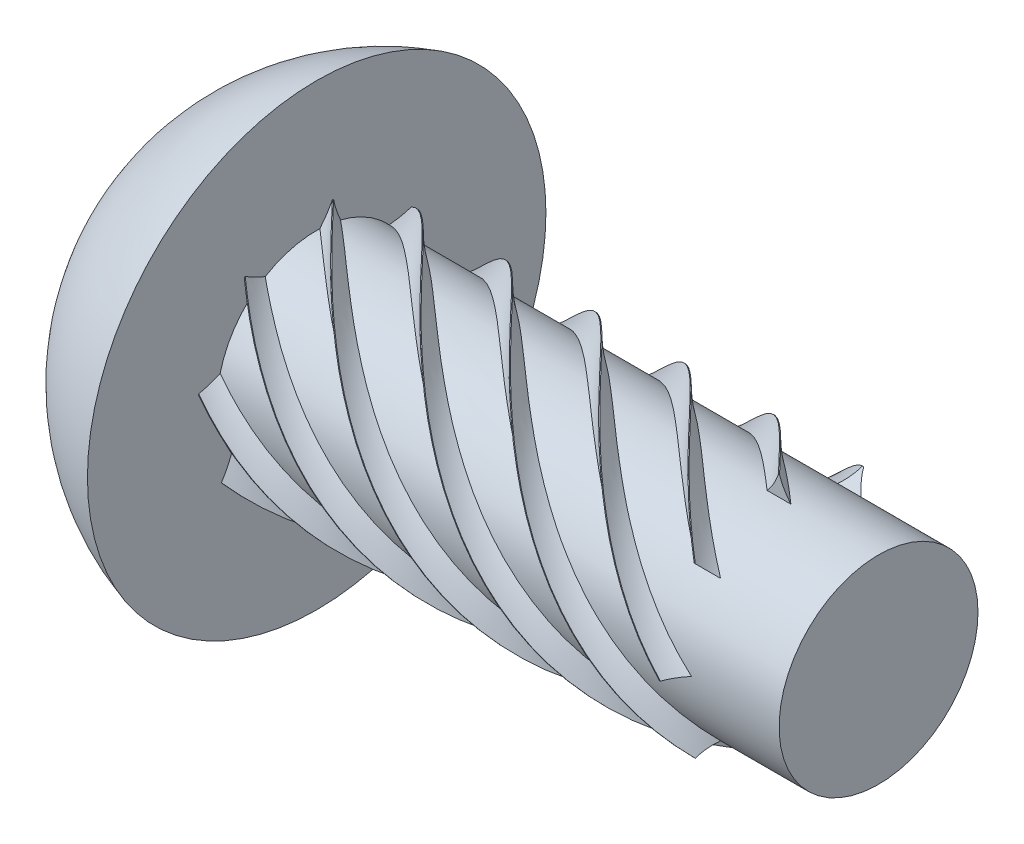
SolidWorks part; units mm, degrees
material "AISI 1020"
ref_plane "Front Plane" through (0, 0, 0) normal (0, 0, 1) x (1, 0, 0)
ref_plane "Top Plane" through (0, 0, 0) normal (0, 1, 0) x (1, 0, 0)
ref_plane "Right Plane" through (0, 0, 0) normal (1, 0, 0) x (0, 0, -1)
sketch "Sketch1" plane through (0, 0, 0) normal (0, 0, 1) x (1, 0, 0)
  line L0 (8.2931, 0) -> (-8.2931, 0) construction
  line L1 (8.2931, -2.2479) -> (8.2931, 2.2479) construction
  line L2 (6.3119, -2.6924) -> (6.3119, 2.6924) construction
  line L3 (-4.4069, -5.1816) -> (-4.4069, 5.1816) construction
  line L4 (0, -101.6) -> (0, 101.6) construction
  point P4 (0, 0)
  point P7 (8.2931, 0)
  point P11 (6.3119, 0)
  point P14 (-4.4069, 0)
  point P17 (0, 0)
  dimension "Shank Diameter" = 5.3848
  dimension "Head Diameter" = 10.3632
  dimension "Head Height" = 3.8862
  dimension "Pilot Diameter" = 4.4958
  dimension "Length" = 12.7
  dimension "Pilot Length" = 1.9812
  dimension "Number of Thread Starts" = 203.2
sketch "Sketch2" plane through (0, 0, 0) normal (0, 0, 1) x (1, 0, 0)
  line L0 (6.3119, -2.6924) -> (6.3119, 2.6924) construction
  line L1 (8.2931, 0) -> (-8.2931, 0) construction
  line L2 (8.2931, 0) -> (8.2931, 2.2479)
  line L3 (8.2931, 2.2479) -> (6.3119, 2.2479)
  line L4 (8.2931, 0) -> (-8.2931, 0) construction
  line L5 (-4.4069, 2.6924) -> (-4.4069, 5.1816)
  line L8 (6.3119, 2.2479) -> (6.3119, 2.6924)
  line L9 (6.3119, 2.6924) -> (-4.4069, 2.6924)
  line L10 (-3.6132, -2.6924) -> (-3.6132, 2.6924) construction
  line L11 (-8.2931, 0) -> (8.2931, 0)
  arc A0 (-4.4069, 5.1816) -> (-8.2931, 0) centre (-2.8956, 0) ccw
  point P7 (-3.6132, -2.6924)
  point P17 (-3.6132, 0)
  dimension "Head Diameter" = 10.3632
  dimension "Head Height" = 3.8862
  dimension "Pilot Diameter" = 4.4958
  dimension "Length" = 12.7
  dimension "D1" = 0.7937
  dimension "Outside Diameter" = 5.3848
revolve "Revolve1" add sketch "Sketch2" angle 360 about L1
sketch "Sketch3" plane through (6.3119, 0, 0) normal (1, 0, 0) x (0, 0, -1)
  circle A0 centre (0, 0) radius 2.6924 construction
  circle A1 centre (0, 0) radius 2.6924
curve "Helix/Spiral1" pitch 16.1544 height 10.7188 turns 0.6635
sketch "Sketch4" plane through (6.3119, 0, 0) normal (1, 0, 0) x (0, 0, -1)
  circle A0 centre (0, 0) radius 2.2479 construction
  circle A1 centre (0, 0) radius 2.6924 construction
  circle A2 centre (0, 0) radius 2.2479
  circle A3 centre (0, 0) radius 2.6924
extrude "Cut-Extrude1" cut sketch "Sketch4" against normal up to surface (10.7188 mm away) up to face at (-4.4069, 0, -5.1816)
sketch "Sketch6" plane through (0, 0, 0) normal (0, 0, 1) x (1, 0, 0)
  line L0 (6.3119, 2.2479) -> (6.0553, 2.6924) construction
  line L1 (5.9016, 2.4701) -> (5.9235, 2.4575) construction
  line L2 (6.0553, 2.6924) -> (6.0299, 2.6924)
  line L3 (6.0299, 2.6924) -> (5.7732, 2.2479) construction
  line L4 (8.2931, 2.2479) -> (-4.4069, 2.2479) construction
  line L5 (5.7732, 2.2479) -> (6.3119, 2.2479)
  line L6 (6.3119, -2.6924) -> (6.3119, 2.6924) construction
  arc A0 (6.0299, 2.6924) -> (5.7732, 2.2479) centre (4.7898, 3.112) cw
  arc A1 (6.0553, 2.6924) -> (6.3119, 2.2479) centre (7.2954, 3.112) ccw
  dimension "D1" = 0.0254
  dimension "D2" = 60
sweep "Sweep1" add profiles "Sketch6" path "Helix/Spiral1"
pattern_circular "CirPattern1" count 8 over 360 of "Sweep1"
equation "\"D3@Helix/Spiral1\"=\"Length@Sketch1\"-\"Pilot Length@Sketch1\""
equation "\"D1@CirPattern1\"=\"Number of Thread Starts@Sketch1\""
equation "\"Head Height@Sketch2\" = \"Head Height@Sketch1\""
equation "\"Head Diameter@Sketch2\" = \"Head Diameter@Sketch1\""
equation "\"Length@Sketch2\" = \"Length@Sketch1\""
equation "\"D4@Helix/Spiral1\" = \"Shank Diameter@Sketch1\" * 3"
equation "\"Outside Diameter@Sketch2\" = \"Shank Diameter@Sketch1\""
equation "\"Pilot Diameter@Sketch2\" = \"Pilot Diameter@Sketch1\""
